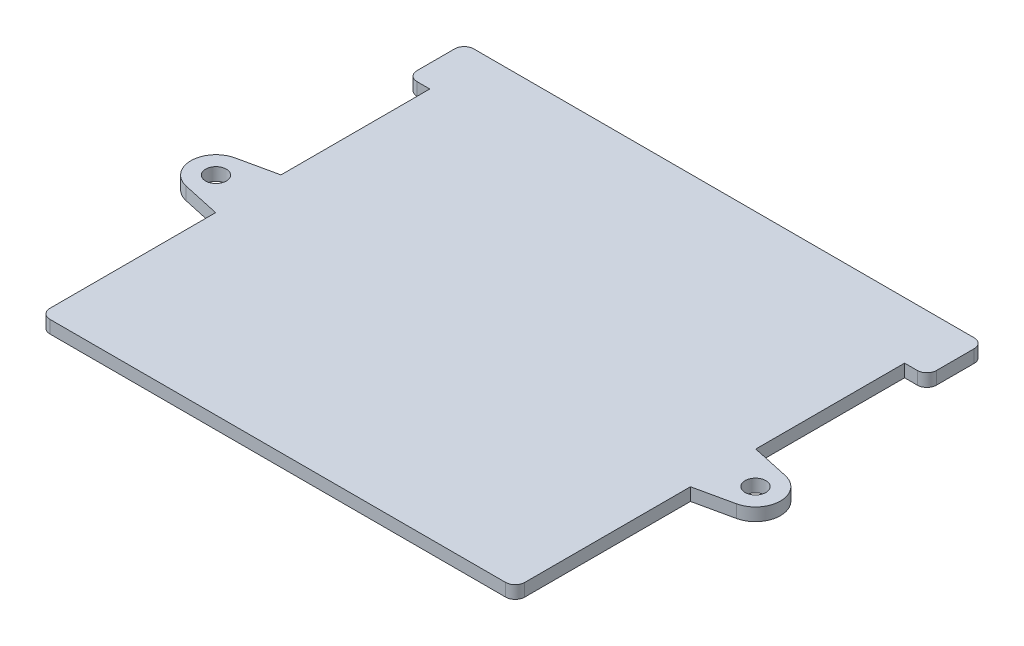
SolidWorks part; units mm, degrees
ref_plane "Front Plane" through (0, 0, 0) normal (0, 0, 1) x (1, 0, 0)
ref_plane "Top Plane" through (0, 0, 0) normal (0, 1, 0) x (1, 0, 0)
ref_plane "Right Plane" through (0, 0, 0) normal (1, 0, 0) x (0, 0, -1)
sketch "Sketch1" plane through (0, 0, 0) normal (0, 1, 0) x (1, 0, 0)
  line L0 (0, 0) -> (0, 140) construction
  line L1 (74.5, 0) -> (-74.5, 0)
  line L2 (-74.5, 0) -> (-74.5, 55)
  line L3 (74.5, 0) -> (74.5, 55)
  line L4 (-74.5, 55) -> (-86.3238, 57.5805)
  line L5 (74.5, 55) -> (86.3238, 57.5805)
  line L6 (-86.3238, 72.9195) -> (-74.5, 75.5)
  line L7 (86.3238, 72.9195) -> (74.5, 75.5)
  line L8 (-74.5, 75.5) -> (-74.5, 122.2)
  line L9 (74.5, 75.5) -> (74.5, 122.2)
  line L10 (-74.5, 122.2) -> (-81.5, 122.2)
  line L11 (74.5, 122.2) -> (81.5, 122.2)
  line L12 (-81.5, 122.2) -> (-81.5, 140)
  line L13 (81.5, 122.2) -> (81.5, 140)
  line L14 (-81.5, 140) -> (81.5, 140)
  arc A0 (-86.3238, 57.5805) -> (-86.3238, 72.9195) centre (-84.65, 65.25) cw
  arc A1 (86.3238, 57.5805) -> (86.3238, 72.9195) centre (84.65, 65.25) ccw
  circle A2 centre (-84.65, 65.25) radius 3.25
  circle A3 centre (84.65, 65.25) radius 3.25
  dimension "D6" = 7.85
  dimension "D10" = 6.5
  dimension "D11" = 6.5
  dimension "D1" = 140
  dimension "D2" = 149
  dimension "D3" = 55
  dimension "D4" = 7
  dimension "D5" = 20.5
  dimension "D7" = 10.15
  dimension "D8" = 10.25
  dimension "D9" = 17.8
extrude "Boss-Extrude1" add sketch "Sketch1" along normal blind 4
fillet "Fillet7" radius 3 6 edges at (74.5, 2, 0) (81.5, 2, -122.2) (81.5, 2, -140) (-81.5, 2, -140) (-81.5, 2, -122.2) (-74.5, 2, 0)
